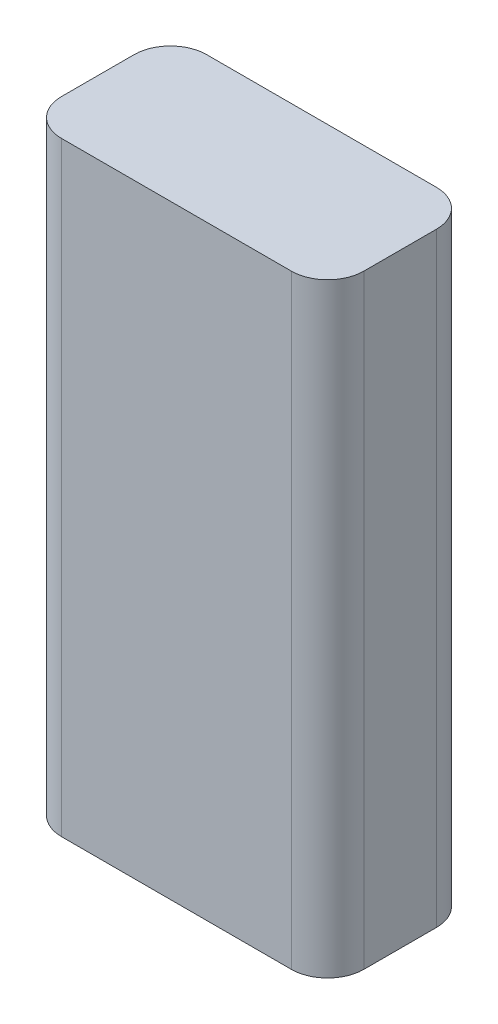
SolidWorks part; units mm, degrees
ref_plane "Front" through (0, 0, 0) normal (0, 0, 1) x (1, 0, 0)
ref_plane "Top" through (0, 0, 0) normal (0, 1, 0) x (1, 0, 0)
ref_plane "Right" through (0, 0, 0) normal (1, 0, 0) x (0, 0, -1)
sketch "Skizze1" plane through (0, 0, 0) normal (0, 1, 0) x (1, 0, 0)
  line L1 (0, 0) -> (25, 0)
  line L2 (0, 0) -> (0, 12)
  line L3 (0, 12) -> (25, 12)
  line L4 (25, 0) -> (25, 12)
  dimension "D1" = 25
  dimension "D2" = 12
extrude "Aufsatz-Linear austragen1" add sketch "Skizze1" along normal blind 50
fillet "Verrundung1" radius 3 4 edges at (0, 25, -12) (25, 25, -12) (25, 25, 0) (0, 25, 0)
